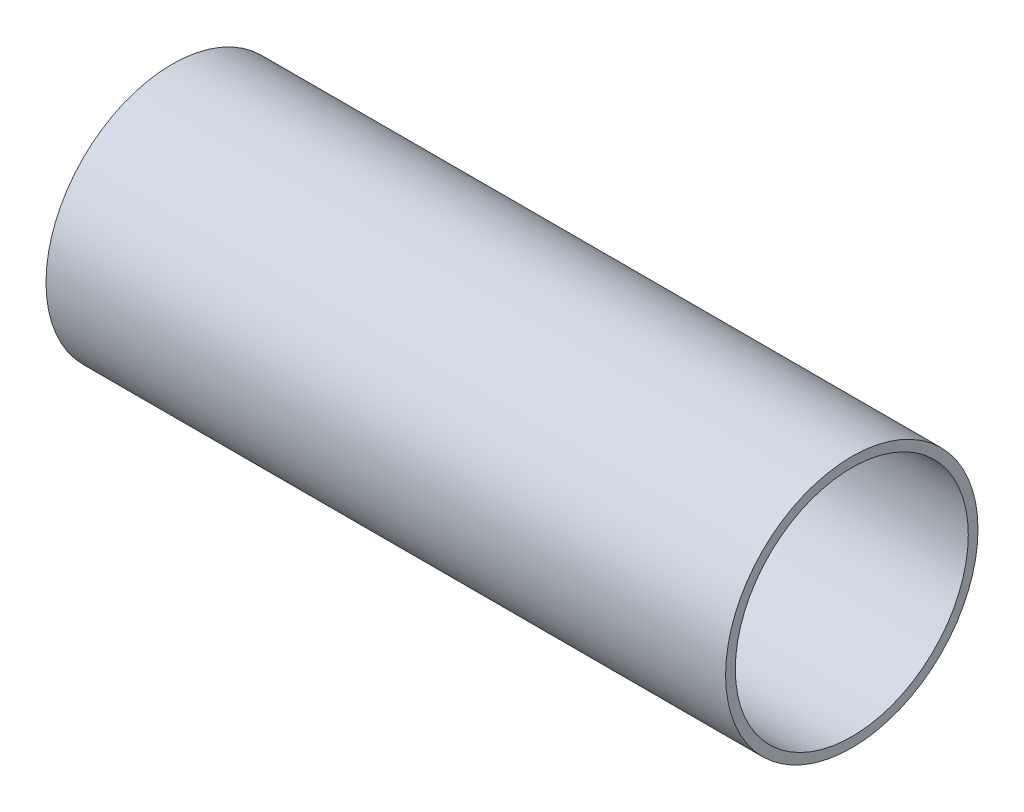
SolidWorks part; units mm, degrees
ref_plane "Front" through (0, 0, 0) normal (0, 0, 1) x (1, 0, 0)
ref_plane "Top" through (0, 0, 0) normal (0, 1, 0) x (1, 0, 0)
ref_plane "Right" through (0, 0, 0) normal (1, 0, 0) x (0, 0, -1)
sketch "Эскиз1" plane through (0, 0, 0) normal (1, 0, 0) x (0, 0, -1)
  circle A0 centre (0, 0) radius 60
  circle A1 centre (0, 0) radius 65
  dimension "D1" = 120
  dimension "D2" = 5
extrude "Бобышка-Вытянуть1" add sketch "Эскиз1" along normal blind 350
